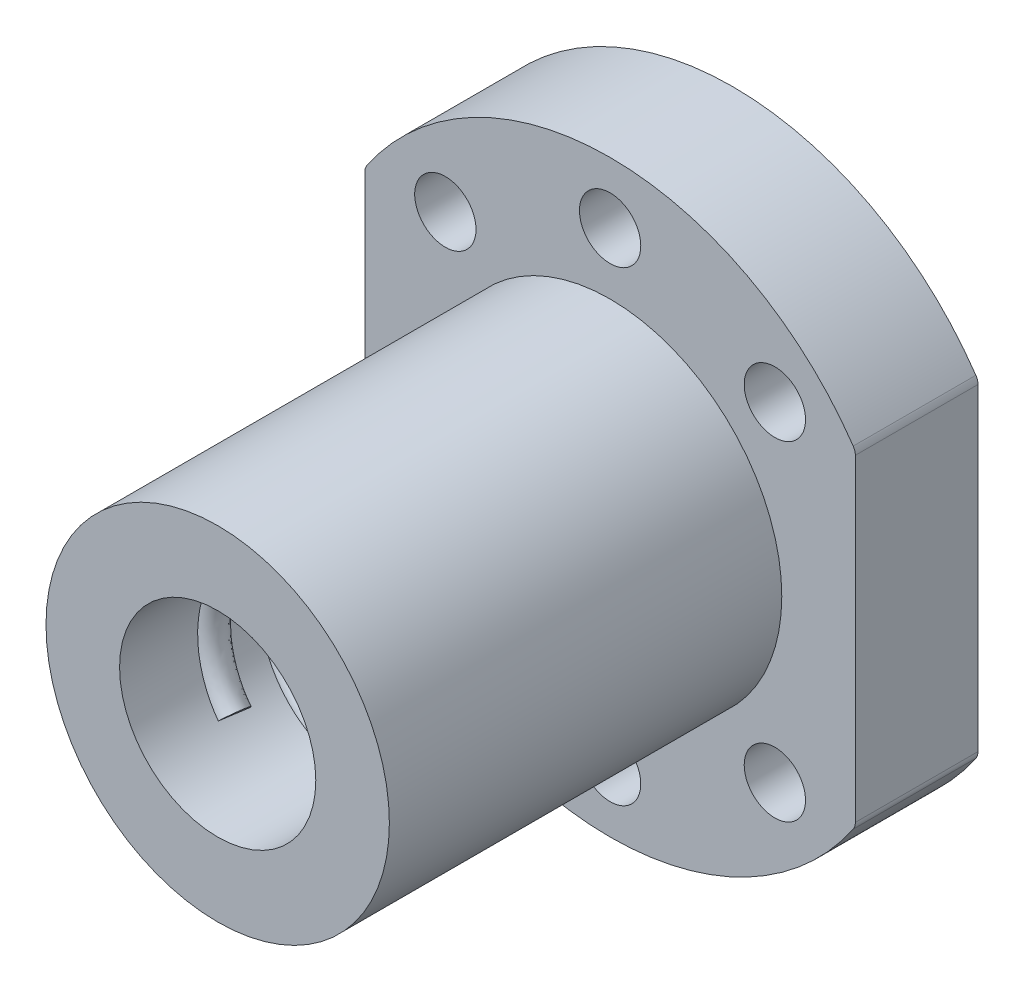
SolidWorks part; units mm, degrees
ref_plane "Front Plane" through (0, 0, 0) normal (0, 0, 1) x (1, 0, 0)
ref_plane "Top Plane" through (0, 0, 0) normal (0, 1, 0) x (1, 0, 0)
ref_plane "Right Plane" through (0, 0, 0) normal (1, 0, 0) x (0, 0, -1)
sketch "Sketch1" plane through (0, 0, 0) normal (0, 0, 1) x (1, 0, 0)
  line L0 (35.2983, 0) -> (-35.2983, 0) construction
  line L1 (0, -36.7704) -> (0, 36.7704) construction
  line L2 (0, 0) -> (-13.435, 13.435) construction
  line L3 (0, 0) -> (13.435, 13.435) construction
  line L4 (-20, -13.2665) -> (-20, 13.2665)
  line L5 (20, 13.2665) -> (20, -13.2665)
  arc A0 (-20, -13.2665) -> (20, -13.2665) centre (0, 0) ccw
  circle A1 centre (0, 0) radius 19 construction
  circle A2 centre (0, 0) radius 8
  circle A3 centre (-13.435, 13.435) radius 2.5
  circle A4 centre (0, 19) radius 2.5
  circle A5 centre (13.435, 13.435) radius 2.5
  circle A6 centre (13.435, -13.435) radius 2.5
  circle A7 centre (0, -19) radius 2.5
  circle A8 centre (-13.435, -13.435) radius 2.5
  arc A9 (20, 13.2665) -> (-20, 13.2665) centre (0, 0) ccw
  point P8 (0, 0)
  point P11 (0, 0)
  dimension "D1" = 48
  dimension "D2" = 38
  dimension "D3" = 16
  dimension "D6" = 5
  dimension "D7" = 20
  dimension "D4" = 45
  dimension "D5" = 45
  dimension "D8" = 20
extrude "Boss-Extrude1" add sketch "Sketch1" along normal blind 10
sketch "Sketch2" plane through (0, 0, 10) normal (0, 0, 1) x (1, 0, 0)
  circle A0 centre (0, 0) radius 14
  circle A1 centre (0, 0) radius 8
  dimension "D1" = 16
  dimension "D2" = 28
extrude "Boss-Extrude2" add sketch "Sketch2" along normal blind 32
ref_plane "Plane1" through (0, 0, 10) normal (0, 0, 1) x (1, 0, 0)
sketch "Sketch3" plane through (0, 0, 10) normal (0, 0, 1) x (1, 0, 0)
  circle A0 centre (0, 0) radius 8 construction
  circle A1 centre (0, 0) radius 8
curve "Helix/Spiral1" pitch 5 height 25 turns 5
ref_plane "Plane2" through (-5.6569, -5.6569, 10) normal (0.7036, -0.7036, 0.099) x (0.07, -0.07, -0.9951)
sketch "Sketch4" plane through (-5.6569, -5.6569, 10) normal (0.7036, -0.7036, 0.099) x (0.07, -0.07, -0.9951)
  line L0 (0, 0) -> (0, 4.6841) construction
  line L1 (0, 0) -> (0, -2.9335) construction
  circle A0 centre (0, -0.3) radius 1.25
  ellipse E0 centre (0, 8) end of major axis (0, 16) minor radius 0.7919 construction
  dimension "D1" = 2.5
  dimension "D2" = 0.3
sweep "Sweep1" add profiles "Sketch4" path "Helix/Spiral1"
fillet "Fillet1" radius 1 4 edges at (20, 13.2665, 5) (20, -13.2665, 5) (-20, -13.2665, 5) (-20, 13.2665, 5)
sketch "Sketch5" plane through (0, 0, 42) normal (0, 0, 1) x (1, 0, 0)
  line L0 (0, -30.8964) -> (0, 30.8964) construction
  line L1 (-28.7942, 0) -> (28.7942, 0) construction
  line L2 (-20, -24) -> (-20, 24)
  line L3 (-20, 12.9615) -> (-20, -12.9615) construction
  line L4 (0, 24) -> (-20, 24)
  line L5 (0, 24) -> (20, 24)
  line L6 (20, 8.5) -> (20, 24)
  line L7 (20, -12.9615) -> (20, 12.9615) construction
  line L8 (20, -8.5) -> (20, -24)
  line L9 (0, -24) -> (20, -24)
  line L10 (0, -24) -> (-20, -24)
  line L11 (20, -8.5) -> (11.1872, -8.5)
  line L12 (20, 8.5) -> (11.1872, 8.5)
  arc A0 (11.1872, 8.5) -> (11.1872, -8.5) centre (0, 0) ccw
  arc A1 (19.8261, 13.525) -> (-19.8261, 13.525) centre (0, 0) ccw construction
  point P6 (0, 0)
  point P9 (0, 0)
  point P27 (-20, 0)
  dimension "D1" = 28.1
  dimension "D2" = 8.5
